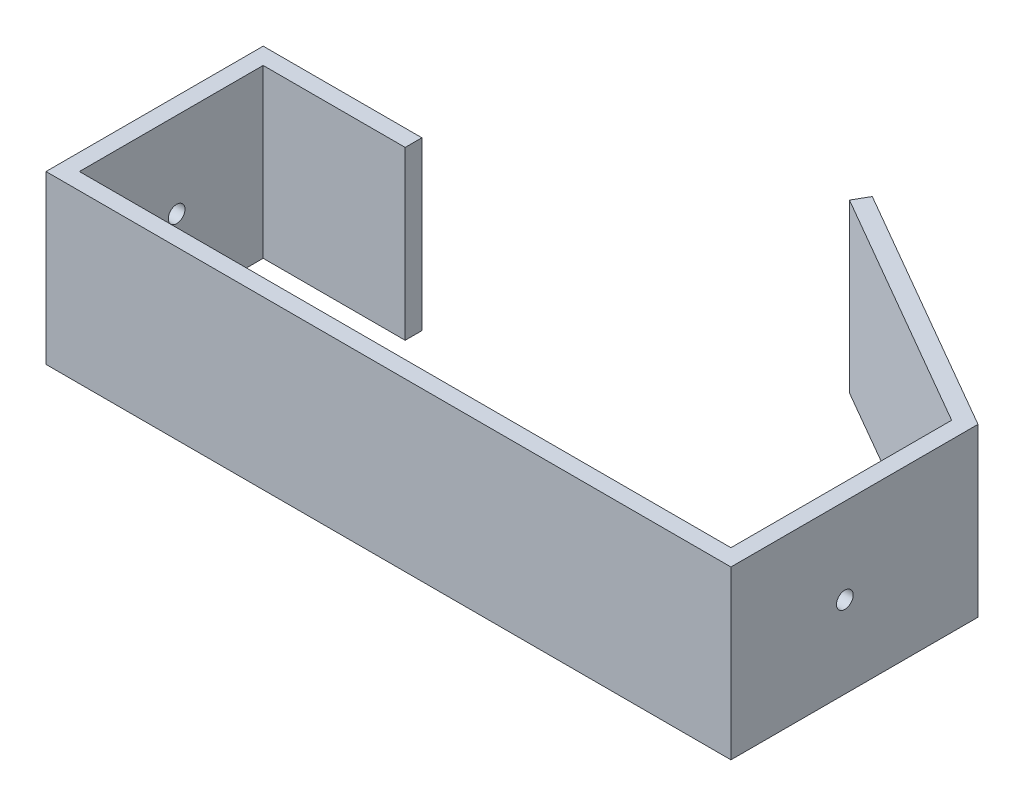
SolidWorks part; units mm, degrees
ref_plane "Front Plane" through (0, 0, 0) normal (0, 0, 1) x (1, 0, 0)
ref_plane "Top Plane" through (0, 0, 0) normal (0, 1, 0) x (1, 0, 0)
ref_plane "Right Plane" through (0, 0, 0) normal (1, 0, 0) x (0, 0, -1)
sketch "Sketch3" plane through (0, 0, 0) normal (0, 1, 0) x (1, 0, 0)
  line L0 (0, 0) -> (73.6122, -42.5)
  line L1 (73.6122, -42.5) -> (73.6122, -112.5)
  line L2 (73.6122, -112.5) -> (-126.3878, -112.5)
  line L3 (-126.3878, -112.5) -> (-126.3878, -52.5)
  line L4 (-126.3878, -52.5) -> (-81.3878, -52.5)
  dimension "D1" = 70
  dimension "D2" = 200
  dimension "D3" = 60
  dimension "D4" = 45
  dimension "D5" = 120
  dimension "D6" = 85
extrude "Extrude-Thin1" add sketch "Sketch3" along normal blind 50 thin thin type mid plane wall 5
sketch "Sketch4" plane through (76.1122, 0, 0) normal (1, 0, 0) x (0, 0, -1)
  circle A0 centre (-80.9097, 24.4517) radius 2.5
  dimension "D1" = 5
extrude "Cut-Extrude3" cut sketch "Sketch4" against normal through all
